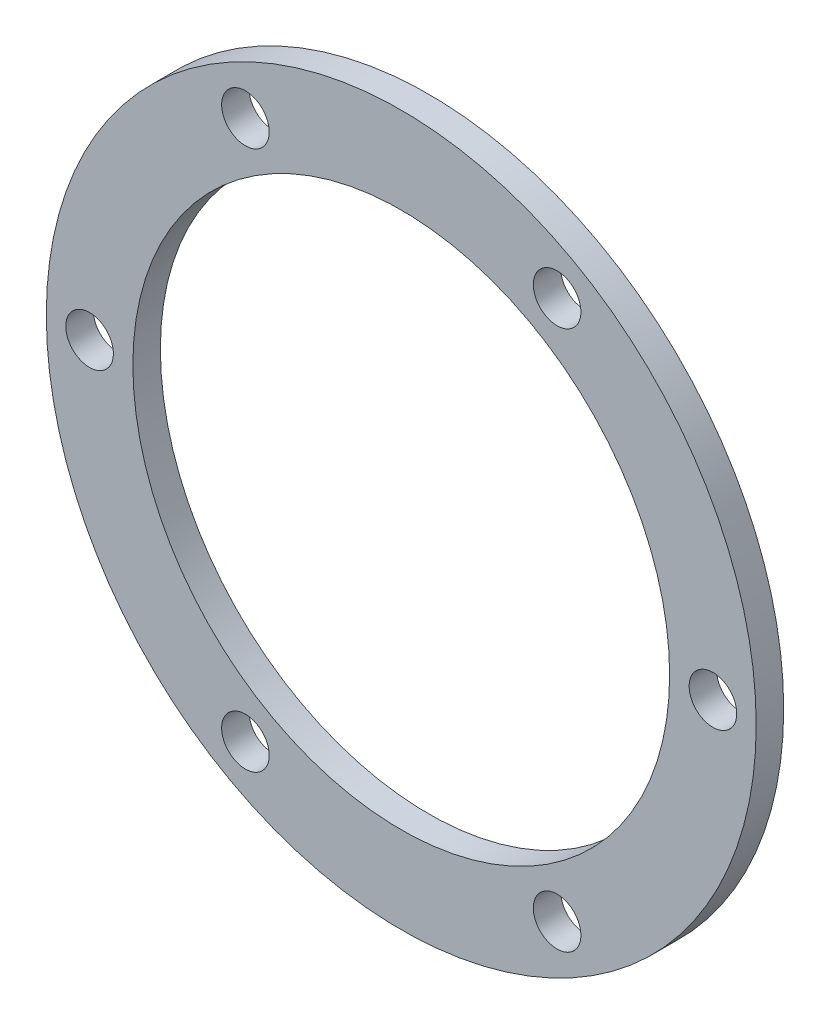
SolidWorks part; units mm, degrees
ref_plane "Front Plane" through (0, 0, 0) normal (0, 0, 1) x (1, 0, 0)
ref_plane "Top Plane" through (0, 0, 0) normal (0, 1, 0) x (1, 0, 0)
ref_plane "Right Plane" through (0, 0, 0) normal (1, 0, 0) x (0, 0, -1)
sketch "Sketch1" plane through (0, 0, 0) normal (0, 0, 1) x (1, 0, 0)
  circle A0 centre (0, 0) radius 31
  circle A1 centre (0, 0) radius 41
  dimension "D1" = 82
  dimension "D2" = 62
extrude "Boss-Extrude1" add sketch "Sketch1" along normal blind 3.175
sketch "Sketch2" plane through (0, 0, 3.175) normal (0, 0, 1) x (1, 0, 0)
  line L0 (0, 0) -> (0, 41) construction
  line L1 (0, 0) -> (-20.5, 35.507) construction
  circle A0 centre (0, 0) radius 41 construction
  circle A1 centre (-18, 31.1769) radius 2.75
  circle A2 centre (18, 31.1769) radius 2.75
  circle A3 centre (36, 0) radius 2.75
  circle A4 centre (18, -31.1769) radius 2.75
  circle A5 centre (-18, -31.1769) radius 2.75
  circle A6 centre (-36, 0) radius 2.75
  point P22 (0, 0)
  dimension "D2" = 5.5
  dimension "D1" = 30
  dimension "D4" = 36
  dimension "D3" = 6
extrude "Cut-Extrude2" cut sketch "Sketch2" against normal through all
